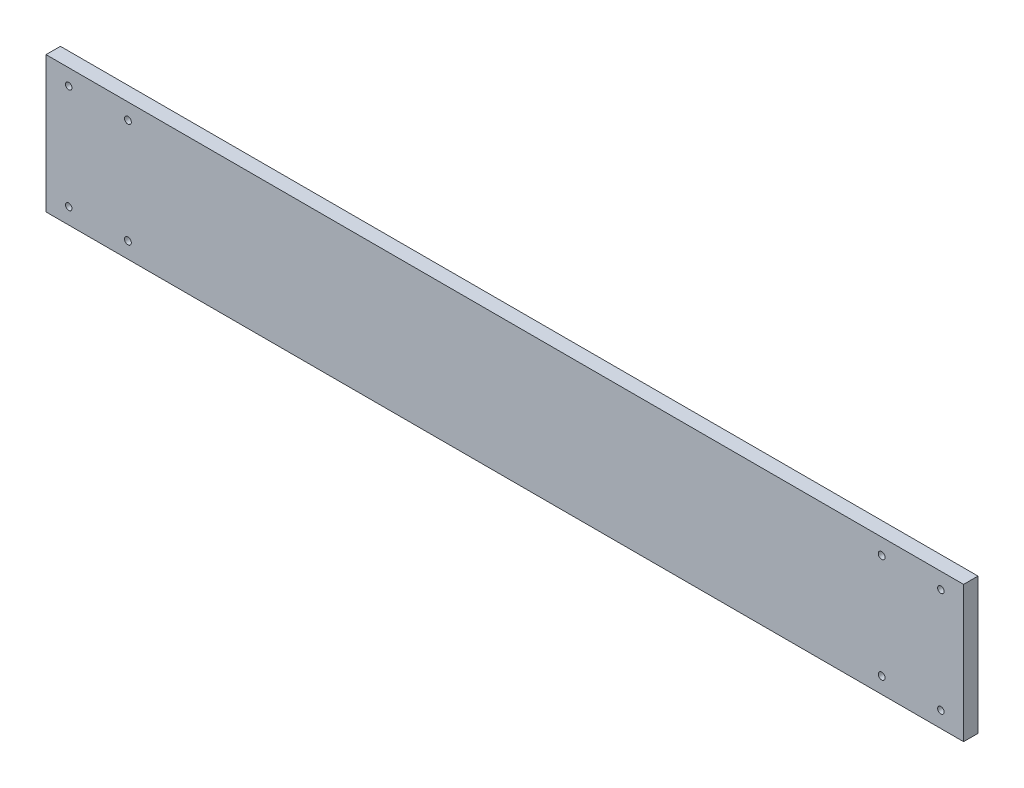
SolidWorks part; units mm, degrees
ref_plane "Front Plane" through (0, 0, 0) normal (0, 0, 1) x (1, 0, 0)
ref_plane "Top Plane" through (0, 0, 0) normal (0, 1, 0) x (1, 0, 0)
ref_plane "Right Plane" through (0, 0, 0) normal (1, 0, 0) x (0, 0, -1)
sketch "Sketch1" plane through (0, 0, 0) normal (0, 0, 1) x (1, 0, 0)
  line L1 (-202.0251, 78.1485) -> (202.0251, 78.1485)
  line L2 (-202.0251, 78.1485) -> (-202.0251, 18.1485)
  line L3 (-202.0251, 18.1485) -> (202.0251, 18.1485)
  line L4 (202.0251, 78.1485) -> (202.0251, 18.1485)
  line L5 (0, 18.1485) -> (0, 78.1485) construction
  line L6 (-202.0251, 48.1485) -> (202.0251, 48.1485) construction
  point P424 (0, 48.1485)
extrude "Boss-Extrude1" add sketch "Sketch1" along normal blind 6.35
sketch "Sketch3" plane through (0, 0, 6.35) normal (0, 0, 1) x (1, 0, 0)
  line L0 (-202.0251, 78.1485) -> (202.0251, 78.1485) construction
  line L1 (202.0251, 78.1485) -> (202.0251, 18.1485) construction
  line L2 (0, 18.1485) -> (0, 78.1485) construction
  line L3 (-202.0251, 48.1485) -> (202.0251, 48.1485) construction
  line L4 (0, 18.1485) -> (0, 78.1485) construction
  line L5 (-202.0251, 48.1485) -> (202.0251, 48.1485) construction
  circle A0 centre (-165.9504, 25.1485) radius 1.5 construction
  circle A1 centre (-165.9504, 71.1485) radius 1.5 construction
  circle A2 centre (165.9504, 25.1485) radius 1.5 construction
  circle A3 centre (165.9504, 71.1485) radius 1.5 construction
  circle A4 centre (-165.9504, 25.1485) radius 1.5
  circle A5 centre (-165.9504, 71.1485) radius 1.5
  circle A6 centre (165.9504, 25.1485) radius 1.5
  circle A7 centre (165.9504, 71.1485) radius 1.5
  circle A8 centre (192.0251, 71.1485) radius 1.425
  circle A9 centre (192.0251, 25.1485) radius 1.425
  circle A10 centre (-192.0251, 25.1485) radius 1.425
  circle A11 centre (-192.0251, 71.1485) radius 1.425
  dimension "D1" = 7
  dimension "D2" = 10
  dimension "D3" = 2.85
extrude "Cut-Extrude1" cut sketch "Sketch3" against normal through all
